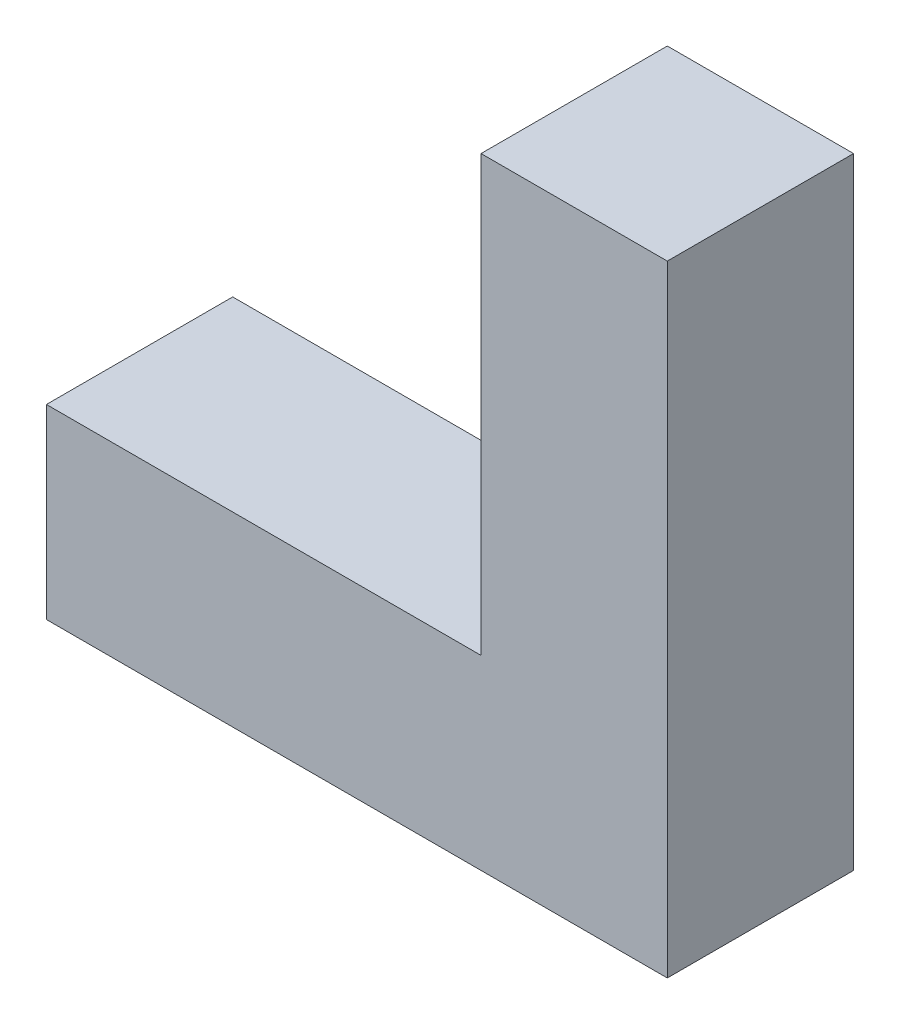
SolidWorks part; units mm, degrees
ref_plane "Front Plane" through (0, 0, 0) normal (0, 0, 1) x (1, 0, 0)
ref_plane "Top Plane" through (0, 0, 0) normal (0, 1, 0) x (1, 0, 0)
ref_plane "Right Plane" through (0, 0, 0) normal (1, 0, 0) x (0, 0, -1)
sketch "Sketch2" plane through (0, 0, 0) normal (0, 0, 1) x (1, 0, 0)
  line L0 (0, 0) -> (-140, 0)
  line L1 (-140, 0) -> (-140, -60)
  line L2 (-140, -60) -> (60, -60)
  line L3 (60, -60) -> (60, 140)
  line L4 (60, 140) -> (0, 140)
  line L5 (0, 140) -> (0, 0)
  dimension "D1" = 140
  dimension "D2" = 60
  dimension "D3" = 60
extrude "Boss-Extrude1" add sketch "Sketch2" along normal blind 60
